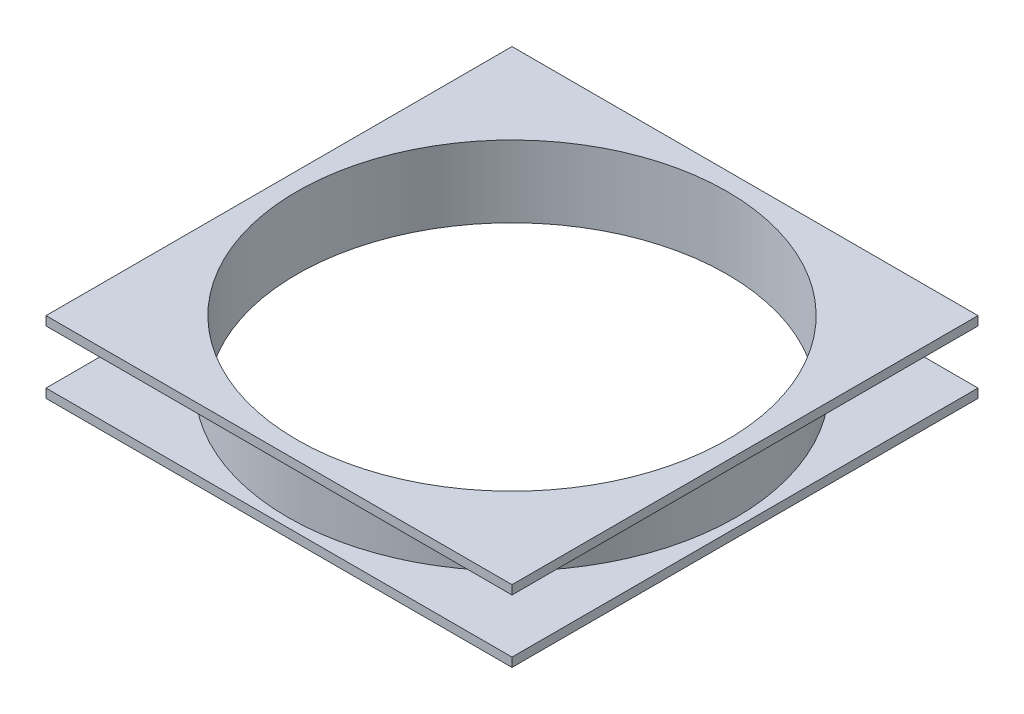
SolidWorks part; units mm, degrees
ref_plane "Front Plane" through (0, 0, 0) normal (0, 0, 1) x (1, 0, 0)
ref_plane "Top Plane" through (0, 0, 0) normal (0, 1, 0) x (1, 0, 0)
ref_plane "Right Plane" through (0, 0, 0) normal (1, 0, 0) x (0, 0, -1)
sketch "Sketch1" plane through (0, 0, 0) normal (0, 1, 0) x (1, 0, 0)
  circle A0 centre (0, 0) radius 60
  circle A1 centre (0, 0) radius 62.5
  dimension "D1" = 120
  dimension "D2" = 2.5
extrude "Boss-Extrude1" add sketch "Sketch1" along normal mid plane 15
sketch "Sketch2" plane through (0, 0, 0) normal (0, 1, 0) x (1, 0, 0)
  line L1 (-65, -65) -> (65, -65)
  line L2 (-65, -65) -> (-65, 65)
  line L3 (-65, 65) -> (65, 65)
  line L4 (65, -65) -> (65, 65)
  line L5 (-65, -65) -> (65, 65) construction
  line L6 (-65, 65) -> (65, -65) construction
  point P0 (0, 0)
  dimension "D1" = 130
sketch "Sketch3" plane through (0, 7.5, 0) normal (0, 1, 0) x (1, 0, 0)
  line L1 (-65, -65) -> (65, -65)
  line L2 (-65, -65) -> (-65, 65)
  line L3 (-65, 65) -> (65, 65)
  line L4 (65, -65) -> (65, 65)
  line L5 (-65, -65) -> (65, 65) construction
  line L6 (-65, 65) -> (65, -65) construction
  circle A0 centre (0, 0) radius 60
  point P0 (0, 0)
extrude "Boss-Extrude2" add sketch "Sketch3" along normal blind 2.5
sketch "Sketch4" plane through (0, -7.5, 0) normal (0, -1, 0) x (1, 0, 0)
  line L1 (-65, -65) -> (65, -65)
  line L2 (-65, -65) -> (-65, 65)
  line L3 (-65, 65) -> (65, 65)
  line L4 (65, -65) -> (65, 65)
  line L5 (-65, -65) -> (65, 65) construction
  line L6 (-65, 65) -> (65, -65) construction
  circle A0 centre (0, 0) radius 60
  point P0 (0, 0)
extrude "Boss-Extrude3" add sketch "Sketch4" along normal blind 2.5
sketch "Sketch5" plane through (0, 10, 0) normal (0, 1, 0) x (1, 0, 0)
  line L0 (-60, 0) -> (0, 0) construction
  line L1 (-115.0998, 30.2688) -> (12.3526, 30.2688) construction
  line L2 (0, 0) -> (-8.5, 14.7224) construction
  line L3 (0, 0) -> (0, 68.9666) construction
  line L4 (0, 0) -> (67.8536, 0) construction
  circle A0 centre (0, 0) radius 60 construction
  circle A1 centre (0, 0) radius 17
  spline S0 degree 2 poles (0, 0) (-30, 60.5377) (-60, 0) knots 0 0 0 1 1 1
  spline S1 degree 2 poles (0, 60) (23.5614, 35.4239) (17, 0) knots 0 0 0 1 1 1
  point P4 (-30, 0)
  point P10 (-8.5, 14.7224)
  point P16 (-30, 30.2688)
  point P18 (-30, 30.2688)
  point P19 (23.5984, 38.8153)
  point P20 (20.1583, 38.7141)
  point P21 (21.7771, 35.4764)
  point P22 (13.1769, 40.6365)
  dimension "D1" = 34
  dimension "D2" = 60
  dimension "D3" = 90
